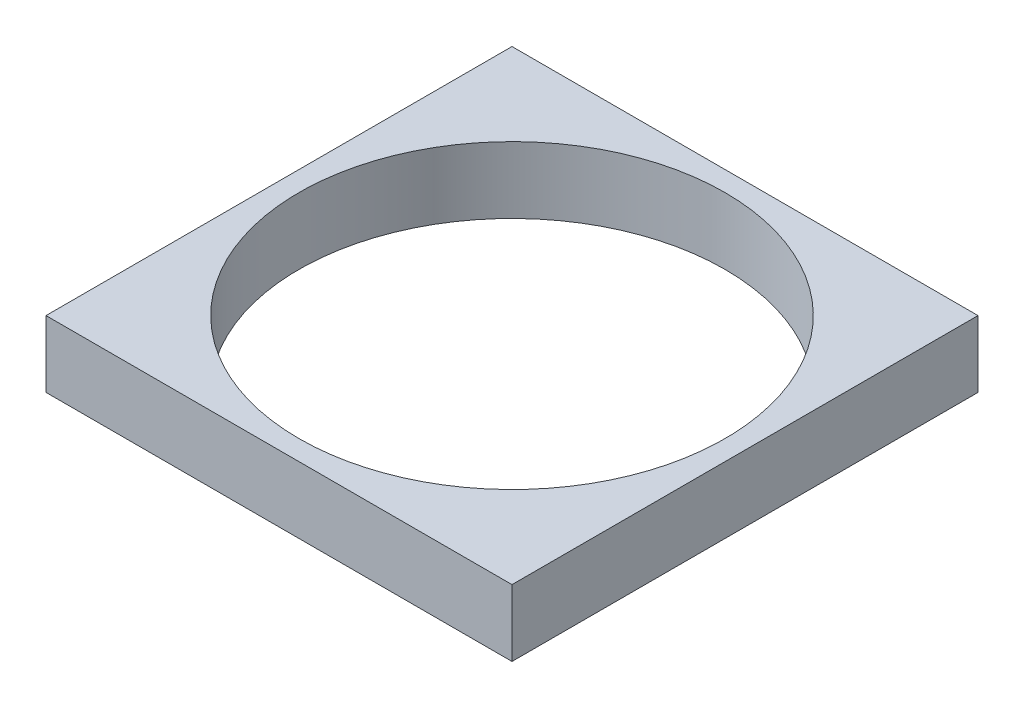
SolidWorks part; units mm, degrees
ref_plane "Front Plane" through (0, 0, 0) normal (0, 0, 1) x (1, 0, 0)
ref_plane "Top Plane" through (0, 0, 0) normal (0, 1, 0) x (1, 0, 0)
ref_plane "Right Plane" through (0, 0, 0) normal (1, 0, 0) x (0, 0, -1)
sketch "Sketch1" plane through (0, 0, 0) normal (0, 1, 0) x (1, 0, 0)
  line L1 (-35, -35) -> (35, -35)
  line L2 (-35, -35) -> (-35, 35)
  line L3 (-35, 35) -> (35, 35)
  line L4 (35, -35) -> (35, 35)
  line L5 (-35, -35) -> (35, 35) construction
  line L6 (-35, 35) -> (35, -35) construction
  circle A0 centre (0, 0) radius 32.004
  point P0 (0, 0)
  dimension "D3" = 64.008
  dimension "D1" = 70
  dimension "D2" = 70
extrude "Boss-Extrude1" add sketch "Sketch1" along normal blind 10
